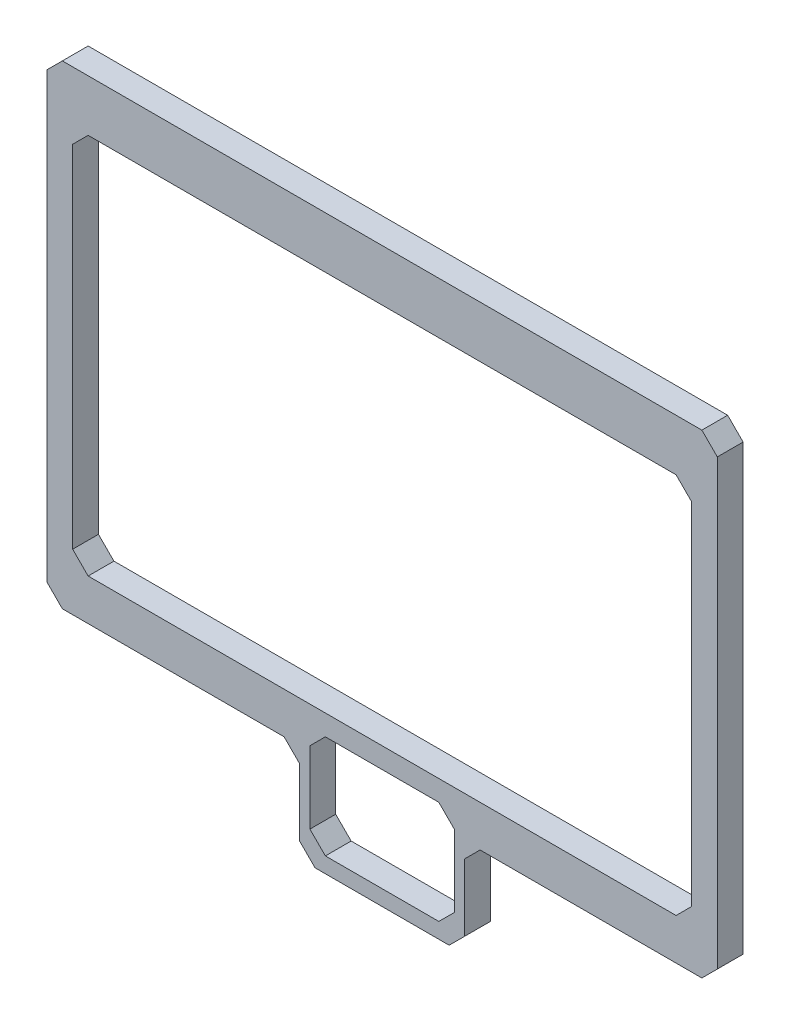
SolidWorks part; units mm, degrees
ref_plane "Front Plane" through (0, 0, 0) normal (0, 0, 1) x (1, 0, 0)
ref_plane "Top Plane" through (0, 0, 0) normal (0, 1, 0) x (1, 0, 0)
ref_plane "Right Plane" through (0, 0, 0) normal (1, 0, 0) x (0, 0, -1)
sketch "Sketch1" plane through (0, 0, 0) normal (0, 0, 1) x (1, 0, 0)
  line L32 (125, -71) -> (125, -3)
  line L33 (5, -71) -> (5, -3)
  line L34 (8, 0) -> (122, 0)
  line L35 (3, 10) -> (127, 10)
  line L36 (130, 7) -> (130, -79)
  line L37 (0, 7) -> (0, -79)
  line L38 (127, -82) -> (84, -82)
  line L39 (46, -82) -> (3, -82)
  line L40 (54, -78) -> (76, -78)
  line L41 (79, -81) -> (79, -95)
  line L42 (76, -98) -> (54, -98)
  line L43 (49, -85) -> (49, -98)
  line L44 (52, -101) -> (78, -101)
  line L45 (81, -98) -> (81, -85)
  line L46 (8, -74) -> (122, -74)
  line L47 (51, -95) -> (51, -81)
  line L48 (0, -79) -> (3, -82)
  line L49 (127, -82) -> (130, -79)
  line L50 (130, 7) -> (127, 10)
  line L51 (3, 10) -> (0, 7)
  line L52 (125, -71) -> (122, -74)
  line L53 (122, 0) -> (125, -3)
  line L54 (5, -3) -> (8, 0)
  line L55 (8, -74) -> (5, -71)
  line L56 (54, -98) -> (51, -95)
  line L57 (79, -95) -> (76, -98)
  line L58 (51, -81) -> (54, -78)
  line L59 (76, -78) -> (79, -81)
  line L60 (81, -85) -> (84, -82)
  line L61 (46, -82) -> (49, -85)
  line L62 (49, -98) -> (52, -101)
  line L63 (78, -101) -> (81, -98)
extrude "Boss-Extrude1" add sketch "Sketch1" along normal blind 5
